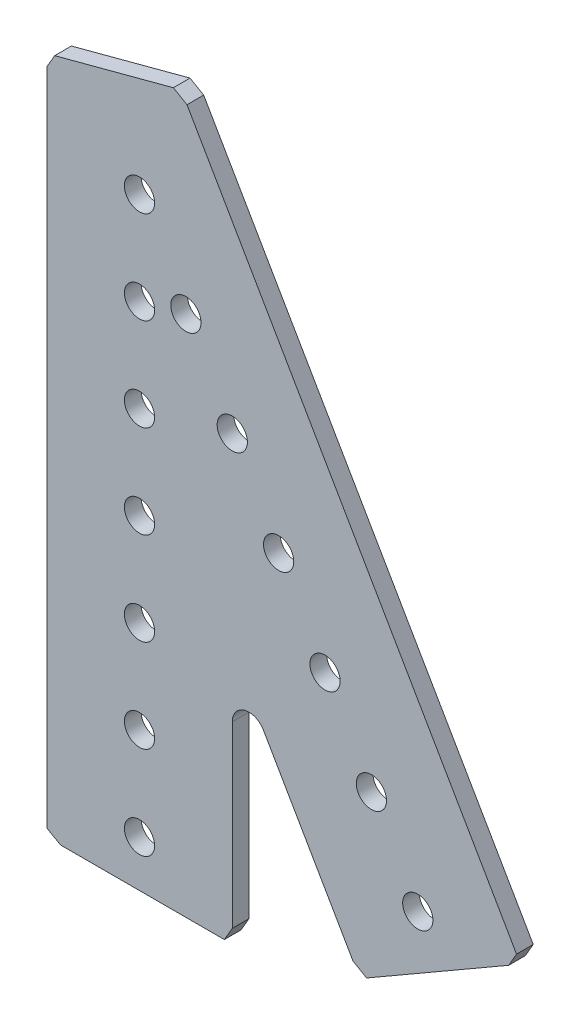
SolidWorks part; units mm, degrees
ref_plane "Front Plane" through (0, 0, 0) normal (0, 0, 1) x (1, 0, 0)
ref_plane "Top Plane" through (0, 0, 0) normal (0, 1, 0) x (1, 0, 0)
ref_plane "Right Plane" through (0, 0, 0) normal (1, 0, 0) x (0, 0, -1)
ref_plane "Plane1" through (0, 0, 0) normal (0, 0, -1) x (-1, 0, 0)
sketch "Sketch1" plane through (0, 0, 0) normal (0, 0, -1) x (-1, 0, 0)
  line L0 (-29.2306, -76.2829) -> (-16.9657, -55.0395)
  line L1 (-12.7, -56.1825) -> (-12.7, -80.6822)
  line L2 (-12.7, -80.6822) -> (-11.6171, -82.55)
  line L3 (-11.6171, -82.55) -> (10.8322, -82.55)
  line L4 (10.8322, -82.55) -> (12.7, -81.4671)
  line L5 (12.7, -81.4671) -> (12.7, 8.7795)
  line L6 (12.7, 8.7795) -> (11.6171, 10.6473)
  line L7 (11.6171, 10.6473) -> (-4.6327, 14.9698)
  line L8 (-4.6327, 14.9698) -> (-6.5005, 13.8869)
  line L9 (-6.5005, 13.8869) -> (-51.6255, -64.272)
  line L10 (-51.6255, -64.272) -> (-50.5426, -66.1398)
  line L11 (-50.5426, -66.1398) -> (-31.0984, -77.3658)
  line L12 (-31.0984, -77.3658) -> (-29.2306, -76.2829)
  arc A0 (-16.9657, -55.0395) -> (-12.7, -56.1825) centre (-14.986, -56.1825) cw
  circle A1 centre (-38.1, -65.9911) radius 2.0701
  circle A2 centre (0, -63.5) radius 2.0701
  circle A3 centre (-25.4, -43.9941) radius 2.0701
  circle A4 centre (-12.7, -21.997) radius 2.0701
  circle A5 centre (0, -38.1) radius 2.0701
  circle A6 centre (0, -12.7) radius 2.0701
  circle A7 centre (0, 0) radius 2.0701
  circle A8 centre (-6.35, -10.9985) radius 2.0701
  circle A9 centre (0, -25.4) radius 2.0701
  circle A10 centre (0, -50.8) radius 2.0701
  circle A11 centre (-19.05, -32.9956) radius 2.0701
  circle A12 centre (-31.75, -54.9926) radius 2.0701
  circle A13 centre (0, -76.2) radius 2.0701
extrude "Boss-Extrude1" add sketch "Sketch1" against normal blind 2.286
